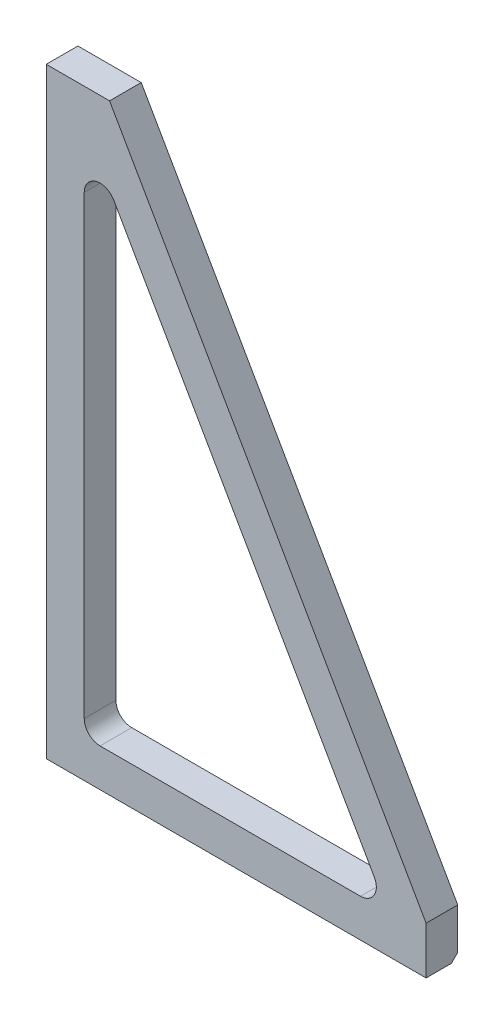
SolidWorks part; units mm, degrees
ref_plane "Front" through (0, 0, 0) normal (0, 0, 1) x (1, 0, 0)
ref_plane "Top" through (0, 0, 0) normal (0, 1, 0) x (1, 0, 0)
ref_plane "Right" through (0, 0, 0) normal (1, 0, 0) x (0, 0, -1)
sketch "Sketch1" plane through (0, 0, 0) normal (0, 0, 1) x (1, 0, 0)
  line L0 (15.24, 21.59) -> (15.24, 204.4515)
  line L1 (0, 0) -> (152.4, 0)
  line L2 (0, 0) -> (0, 241.3)
  line L3 (0, 241.3) -> (25.4, 241.3)
  line L4 (152.4, 0) -> (152.4, 19.05)
  line L7 (21.59, 15.24) -> (126.0823, 15.24)
  line L8 (25.4, 241.3) -> (152.4, 19.05)
  line L9 (27.1033, 207.6019) -> (131.5956, 24.7405)
  arc A0 (131.5956, 24.7405) -> (126.0823, 15.24) centre (126.0823, 21.59) cw
  arc A3 (15.24, 21.59) -> (21.59, 15.24) centre (21.59, 21.59) ccw
  arc A4 (15.24, 204.4515) -> (27.1033, 207.6019) centre (21.59, 204.4515) cw
  dimension "D4" = 6.35
  dimension "D8" = 6.35
  dimension "D9" = 6.35
  dimension "D1" = 152.4
  dimension "D2" = 241.3
  dimension "D5" = 19.05
  dimension "D6" = 25.4
  dimension "D3" = 15.24
  dimension "D7" = 15.24
extrude "Base-Extrude" add sketch "Sketch1" along normal blind 12.7
chamfer "Chamfer3" distance 2.54 angle 45 1 edges at (76.2, 0, 0)
